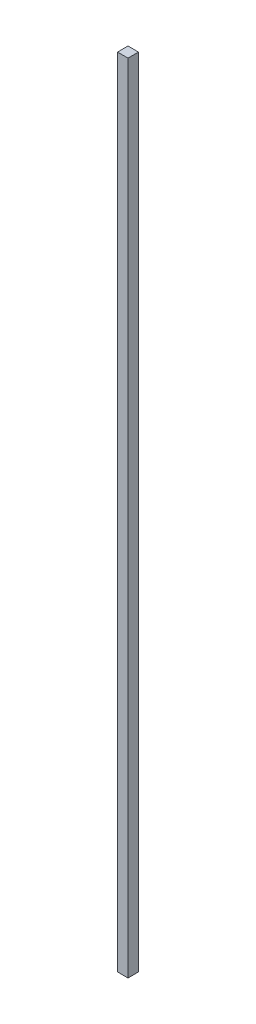
SolidWorks part; units mm, degrees
ref_plane "Front Plane" through (0, 0, 0) normal (0, 0, 1) x (1, 0, 0)
ref_plane "Top Plane" through (0, 0, 0) normal (0, 1, 0) x (1, 0, 0)
ref_plane "Right Plane" through (0, 0, 0) normal (1, 0, 0) x (0, 0, -1)
sketch "Sketch1" plane through (0, 0, 0) normal (0, 1, 0) x (1, 0, 0)
  line L0 (0, 0) -> (0, 3.175)
  line L1 (0, 3.175) -> (3.175, 3.175)
  line L2 (3.175, 3.175) -> (3.175, 0)
  line L3 (3.175, 0) -> (0, 0)
  dimension "D1" = 3.175
extrude "Boss-Extrude1" add sketch "Sketch1" along normal blind 241.3
